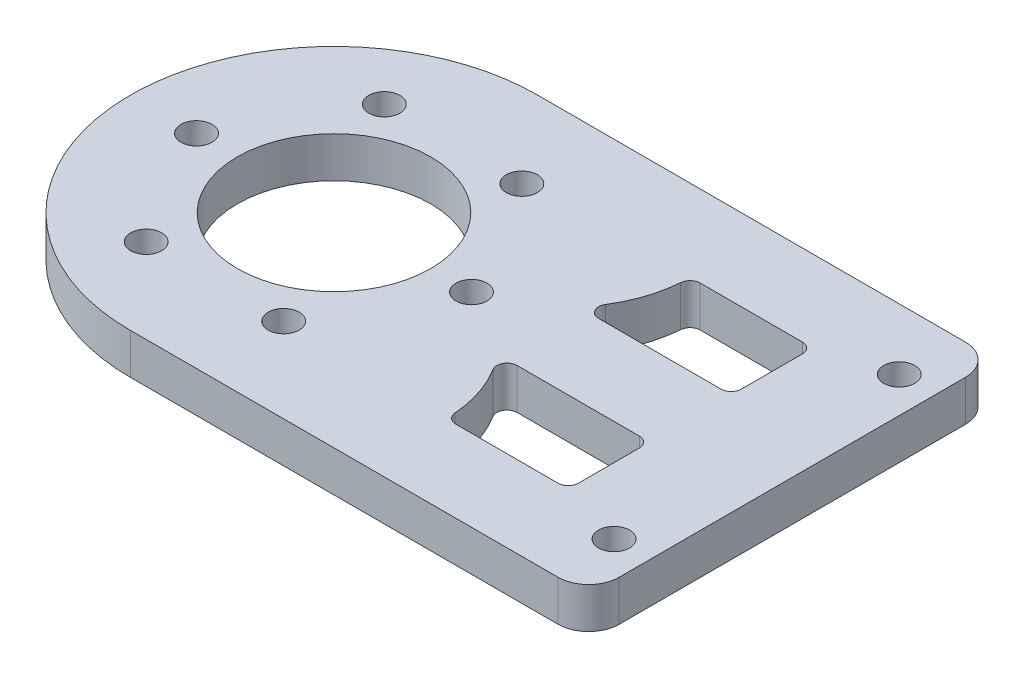
SolidWorks part; units mm, degrees
material "Thornel Mat VMA"
ref_plane "前视基准面" through (0, 0, 0) normal (0, 0, 1) x (1, 0, 0)
ref_plane "上视基准面" through (0, 0, 0) normal (0, 1, 0) x (1, 0, 0)
ref_plane "右视基准面" through (0, 0, 0) normal (1, 0, 0) x (0, 0, -1)
other "Configuration Table"
sketch "草图1" plane through (0, 0, 0) normal (0, 1, 0) x (1, 0, 0)
  line L1 (-22.5, -20) -> (22.5, -20)
  line L2 (-22.5, -20) -> (-22.5, 20)
  line L3 (-22.5, 20) -> (22.5, 20)
  line L4 (22.5, -20) -> (22.5, 20)
  line L5 (-22.5, -20) -> (22.5, 20) construction
  line L6 (-22.5, 20) -> (22.5, -20) construction
  circle A0 centre (-22.5, 0) radius 20
  point P0 (0, 0)
  dimension "D1" = 40
  dimension "D2" = 45
extrude "凸台-拉伸1" add sketch "草图1" along normal blind 4 contours L2 A0 | L2 A0 | A0 L1 L4 L3
sketch "草图3" plane through (0, 0, 0) normal (0, 1, 0) x (1, 0, 0)
  circle A0 centre (-22.5, 0) radius 13.5 construction
  circle A1 centre (-36, 0) radius 1.525
  circle A2 centre (-29.25, 11.6913) radius 1.525
  circle A3 centre (-15.75, 11.6913) radius 1.525
  circle A4 centre (-9, 0) radius 1.525
  circle A5 centre (-15.75, -11.6913) radius 1.525
  circle A6 centre (-29.25, -11.6913) radius 1.525
  point P17 (-22.5, 0)
  dimension "D1" = 27
  dimension "D2" = 3.05
  dimension "D3" = 6
extrude "切除-拉伸3" cut sketch "草图3" along normal through all
sketch "草图4" plane through (0, 0, 0) normal (0, -1, 0) x (1, 0, 0)
  circle A0 centre (-19, 0) radius 10
  dimension "D1" = 20
sketch "草图6" plane through (0, 0, 0) normal (0, -1, 0) x (1, 0, 0)
  circle A0 centre (-22.5, 0) radius 9.5
  dimension "D1" = 19
extrude "切除-拉伸5" cut sketch "草图6" against normal through all
fillet "圆角1" radius 3 2 edges at (22.5, 2, -20) (22.5, 2, 20)
sketch "草图7" plane through (0, 4, 0) normal (0, 1, 0) x (1, 0, 0)
  circle A0 centre (19, -14) radius 1.525
  circle A1 centre (19, 14) radius 1.525
  circle A2 centre (19, 14) radius 1.525 construction
  circle A3 centre (19, -14) radius 1.25 construction
  dimension "D1" = 3.05
extrude "切除-拉伸6" cut sketch "草图7" against normal blind 10
sketch "草图8" plane through (0, 0, 0) normal (0, -1, 0) x (1, 0, 0)
  line L0 (0, 0) -> (22.5, 0) construction
  line L1 (22.5, 17) -> (22.5, -17) construction
  line L2 (-2.5, 4) -> (12.5, 4)
  line L3 (12.5, 4) -> (12.5, 12)
  line L4 (12.5, 12) -> (0.5, 12)
  line L5 (-22.5, 20) -> (19.5, 20) construction
  line L6 (12.5, -12) -> (0.5, -12)
  line L7 (12.5, -4) -> (12.5, -12)
  line L8 (-2.5, -4) -> (12.5, -4)
  arc A0 (0.5, 12) -> (-2.5, 4) centre (-11.6667, 12) cw
  arc A1 (0.5, -12) -> (-2.5, -4) centre (-11.6667, -12) ccw
  dimension "D1" = 8
  dimension "D2" = 10
  dimension "D3" = 8
  dimension "D4" = 15
  dimension "D5" = 12
extrude "切除-拉伸7" cut sketch "草图8" against normal blind 10
fillet "圆角2" radius 1 8 edges at (-2.5, 2, -4) (12.5, 2, -4) (12.5, 2, -12) (0.5, 2, -12) (0.5, 2, 12) (12.5, 2, 12) (12.5, 2, 4) (-2.5, 2, 4)
